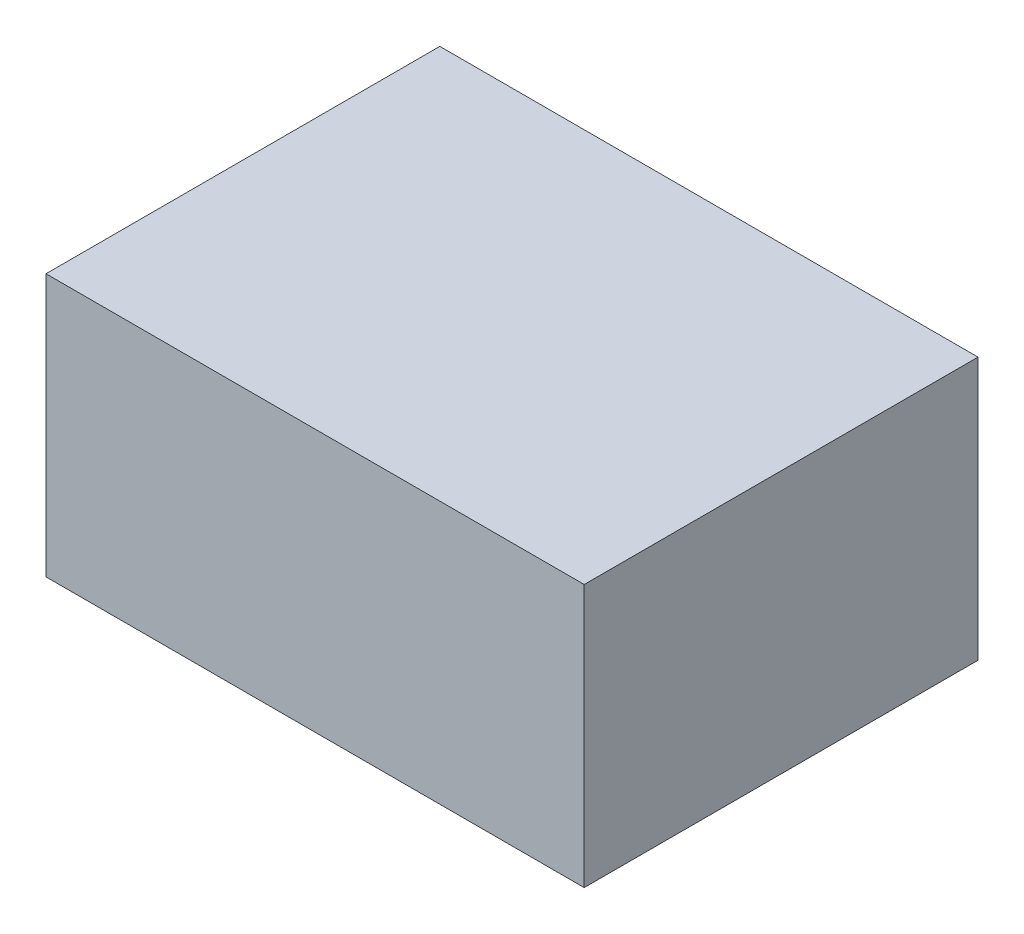
SolidWorks part; units mm, degrees
ref_plane "Alzado" through (0, 0, 0) normal (0, 0, 1) x (1, 0, 0)
ref_plane "Planta" through (0, 0, 0) normal (0, 1, 0) x (1, 0, 0)
ref_plane "Vista lateral" through (0, 0, 0) normal (1, 0, 0) x (0, 0, -1)
sketch "Croquis1" plane through (0, 0, 0) normal (0, 0, 1) x (1, 0, 0)
  line L1 (-20.5, -10) -> (20.5, -10)
  line L2 (-20.5, -10) -> (-20.5, 10)
  line L3 (-20.5, 10) -> (20.5, 10)
  line L4 (20.5, -10) -> (20.5, 10)
  line L5 (-20.5, -10) -> (20.5, 10) construction
  line L6 (-20.5, 10) -> (20.5, -10) construction
  point P0 (0, 0)
extrude "Saliente-Extruir1" add sketch "Croquis1" along normal blind 30
